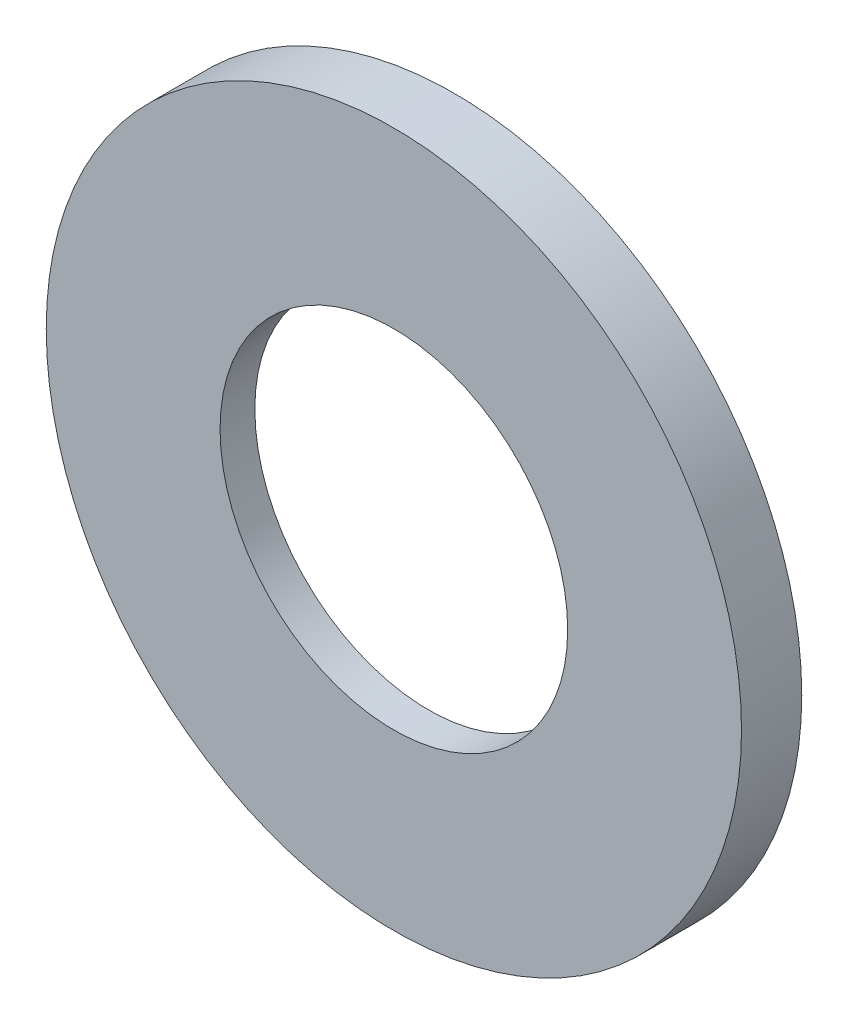
SolidWorks part; units mm, degrees
ref_plane "Plan de face" through (0, 0, 0) normal (0, 0, 1) x (1, 0, 0)
ref_plane "Plan de dessus" through (0, 0, 0) normal (0, 1, 0) x (1, 0, 0)
ref_plane "Plan de droite" through (0, 0, 0) normal (1, 0, 0) x (0, 0, -1)
sketch "Esquisse1" plane through (0, 0, 0) normal (0, 0, 1) x (1, 0, 0)
  circle A0 centre (0, 0) radius 75
  circle A1 centre (0, 0) radius 52.5
  dimension "D1" = 150
  dimension "D2" = 105
extrude "Boss.-Extru.1" add sketch "Esquisse1" along normal blind 30
sketch "Esquisse2" plane through (0, 0, 30) normal (0, 0, 1) x (1, 0, 0)
  circle A0 centre (0, 0) radius 52.5
  circle A1 centre (0, 0) radius 37.5
  dimension "D1" = 75
  dimension "D2" = 105
extrude "Boss.-Extru.2" add sketch "Esquisse2" against normal blind 19.5
sketch "Esquisse3" plane through (0, 0, 10.5) normal (0, 0, -1) x (-1, 0, 0)
  circle A0 centre (0, 0) radius 42.5
  circle A1 centre (0, 0) radius 37.5
  dimension "D1" = 75
  dimension "D2" = 85
extrude "Boss.-Extru.3" add sketch "Esquisse3" along normal blind 5
sketch "Esquisse4" plane through (0, 0, 30) normal (0, 0, 1) x (1, 0, 0)
  circle A0 centre (0, 0) radius 37.5
  circle A1 centre (0, 0) radius 75
extrude "Enlèv. mat.-Extru.1" cut sketch "Esquisse4" against normal blind 17
